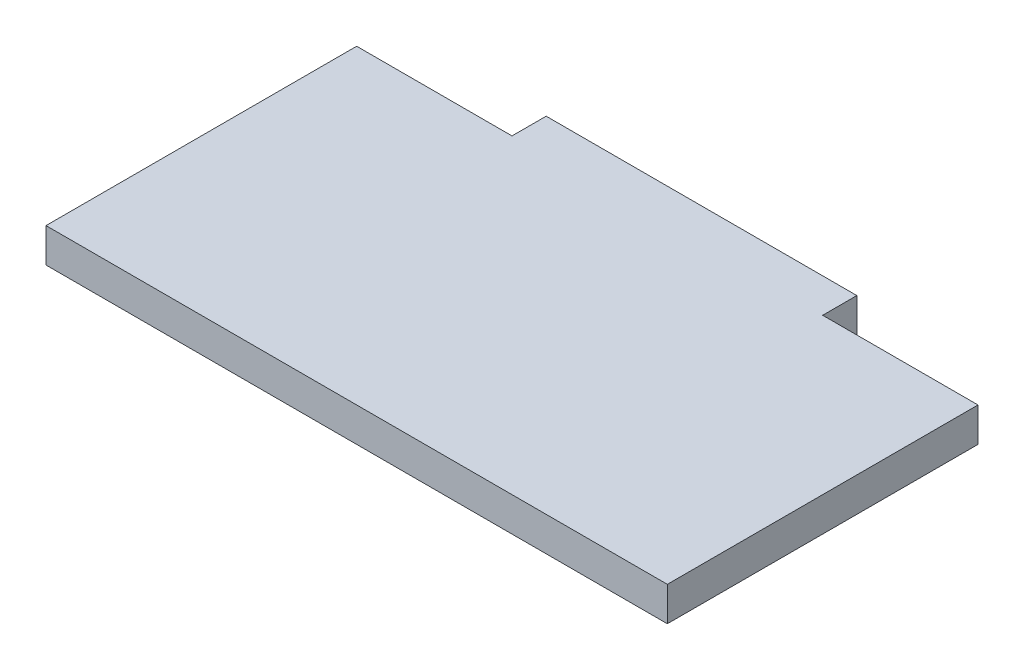
SolidWorks part; units mm, degrees
ref_plane "Front Plane" through (0, 0, 0) normal (0, 0, 1) x (1, 0, 0)
ref_plane "Top Plane" through (0, 0, 0) normal (0, 1, 0) x (1, 0, 0)
ref_plane "Right Plane" through (0, 0, 0) normal (1, 0, 0) x (0, 0, -1)
sketch "Sketch1" plane through (0, 0, 0) normal (0, 1, 0) x (1, 0, 0)
  line L0 (38.1, 25.4) -> (50.8, 25.4)
  line L1 (0, 0) -> (50.8, 0)
  line L2 (0, 0) -> (0, 25.4)
  line L3 (0, 25.4) -> (12.7, 25.4)
  line L4 (50.8, 0) -> (50.8, 25.4)
  line L5 (12.7, 28.194) -> (38.1, 28.194)
  line L6 (12.7, 28.194) -> (12.7, 25.4)
  line L8 (38.1, 28.194) -> (38.1, 25.4)
  dimension "D1" = 25.4
  dimension "D2" = 50.8
  dimension "D3" = 2.794
  dimension "D4" = 25.4
  dimension "D5" = 12.7
extrude "Boss-Extrude1" add sketch "Sketch1" along normal blind 2.794
